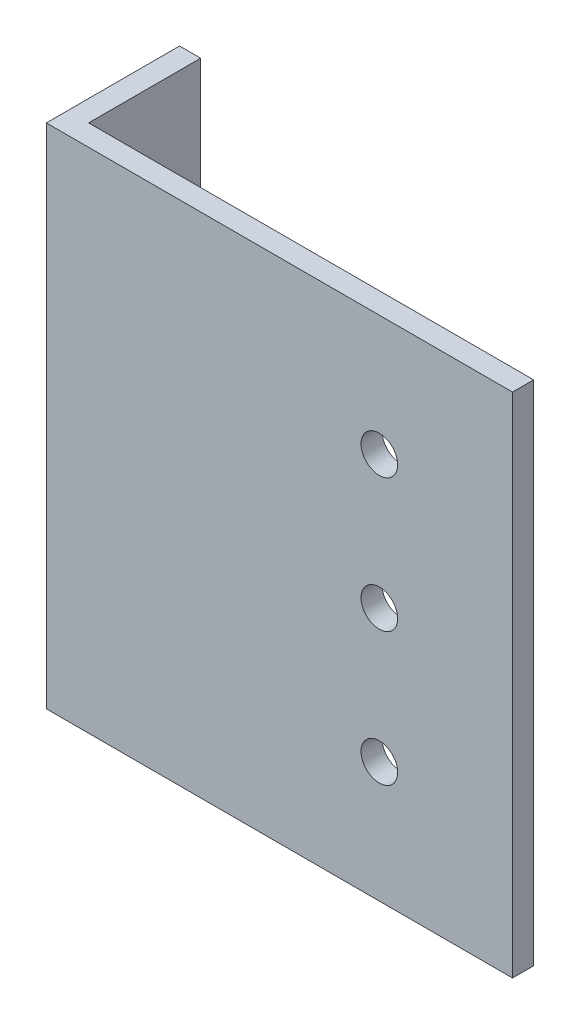
SolidWorks part; units mm, degrees
ref_plane "Front Plane" through (0, 0, 0) normal (0, 0, 1) x (1, 0, 0)
ref_plane "Top Plane" through (0, 0, 0) normal (0, 1, 0) x (1, 0, 0)
ref_plane "Right Plane" through (0, 0, 0) normal (1, 0, 0) x (0, 0, -1)
sketch "Sketch1" plane through (0, 0, 0) normal (0, 1, 0) x (1, 0, 0)
  line L0 (0, 20) -> (0, 0)
  line L1 (0, 0) -> (70, 0)
  dimension "D1" = 20
  dimension "D2" = 70
extrude "Extrude-Thin1" add sketch "Sketch1" along normal mid plane 76.2 thin thin type one direction reverse wall 3.175
hole_wizard "M5 Clearance Hole1" positions "Sketch2" profile "Sketch4" hole size "M5" standard "ANSI Metric" end condition through all
sketch "Sketch2" plane through (0, 0, 0) normal (0, 0, 1) x (1, 0, 0)
  line L0 (70, 38.1) -> (70, -38.1) construction
  point P0 (50, 20)
  point P2 (50, 0)
  point P4 (50, -20)
  dimension "D1" = 20
  dimension "D2" = 20
  dimension "D3" = 20
sketch "Sketch4" plane through (50, 20, 0) normal (1, 0, 0) x (0, -1, 0)
  line L0 (0, 0) -> (0, 20)
  line L1 (0, 20) -> (2.75, 20)
  line L2 (2.75, 20) -> (2.75, 0)
  line L5 (2.75, 0) -> (0, 0)
  line L11 (0, -6.35) -> (0, 107.95) construction
  dimension "Thru Hole Dia." = 5.5
  dimension "Thru Hole Depth" = 20
hole_wizard "M5 Clearance Hole2" positions "Sketch5" profile "Sketch6" hole size "M5" standard "ANSI Metric" end condition through all
sketch "Sketch5" plane through (3.175, 0, 0) normal (1, 0, 0) x (0, 0, -1)
  line L0 (0, 0) -> (20, 0) construction
  line L1 (20, 38.1) -> (20, -38.1) construction
  point P0 (14, 20)
  point P4 (14, -20)
  dimension "D1" = 6
  dimension "D2" = 20
sketch "Sketch6" plane through (3.175, 20, -14) normal (0, 1, 0) x (0, 0, -1)
  line L0 (0, 0) -> (0, 3.175)
  line L1 (0, 3.175) -> (2.75, 3.175)
  line L2 (2.75, 3.175) -> (2.75, 0)
  line L5 (2.75, 0) -> (0, 0)
  line L11 (0, -6.35) -> (0, 107.95) construction
  dimension "Thru Hole Dia." = 5.5
  dimension "Thru Hole Depth" = 3.175
